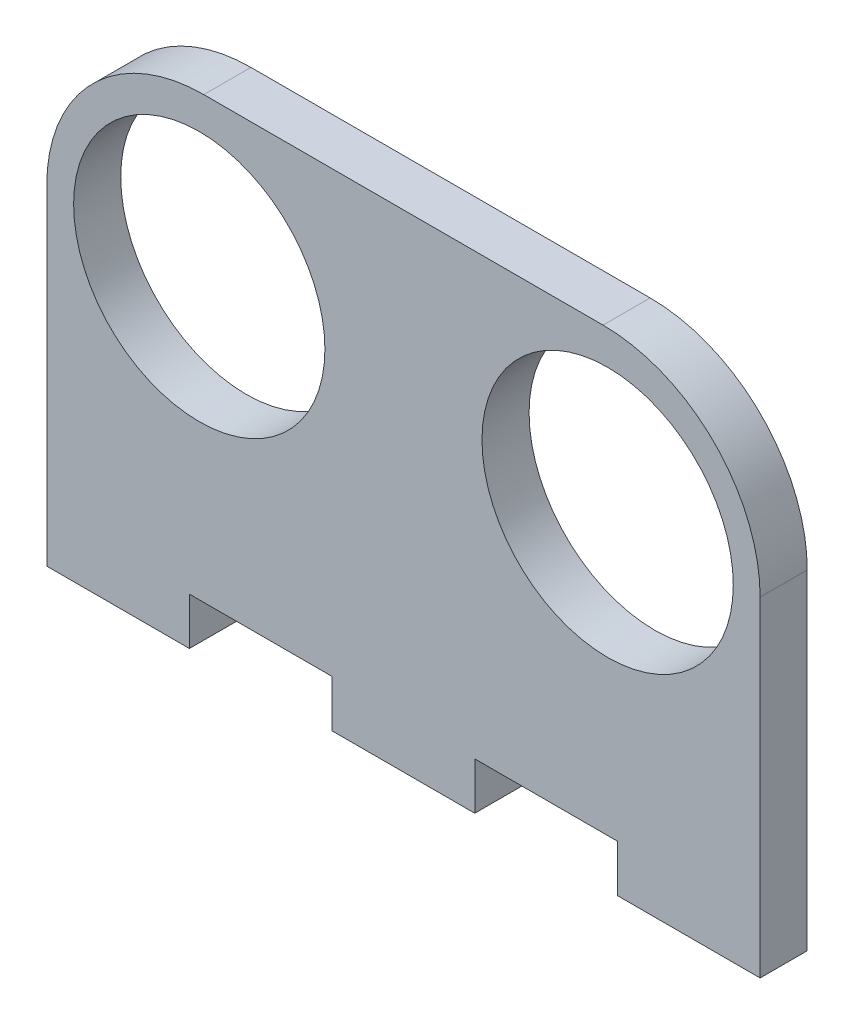
SolidWorks part; units mm, degrees
material "Arce"
ref_plane "Alzado" through (0, 0, 0) normal (0, 0, 1) x (1, 0, 0)
ref_plane "Planta" through (0, 0, 0) normal (0, 1, 0) x (1, 0, 0)
ref_plane "Vista lateral" through (0, 0, 0) normal (1, 0, 0) x (0, 0, -1)
sketch "Croquis1" plane through (0, 0, 0) normal (0, 0, 1) x (1, 0, 0)
  line L1 (-22.71, -10.17) -> (22.71, -10.17)
  line L2 (-22.71, -10.17) -> (-22.71, 7.83)
  line L3 (-12.71, 17.83) -> (12.71, 17.83)
  line L4 (22.71, -10.17) -> (22.71, 7.83)
  line L5 (-22.71, -10.17) -> (22.71, 17.83) construction
  line L6 (-22.71, 17.83) -> (22.71, -10.17) construction
  arc A0 (-22.71, 7.83) -> (-12.71, 17.83) centre (-12.71, 7.83) cw
  arc A1 (12.71, 17.83) -> (22.71, 7.83) centre (12.71, 7.83) cw
  point P0 (0, 3.83)
  dimension "D3" = 10
  dimension "D1" = 28
  dimension "D2" = 45.42
extrude "Saliente-Extruir1" add sketch "Croquis1" along normal blind 3
sketch "Croquis2" plane through (0, 0, 3) normal (0, 0, 1) x (1, 0, 0)
  line L1 (-22.71, 7.83) -> (-22.71, -10.17) construction
  line L2 (12.71, 17.83) -> (-12.71, 17.83) construction
  line L3 (-22.71, -10.17) -> (22.71, -10.17) construction
  line L4 (22.71, -10.17) -> (22.71, 7.83) construction
  circle A0 centre (-21.41, 16.53) radius 0.8
  circle A1 centre (21.41, 16.53) radius 0.8
  circle A2 centre (21.41, -8.87) radius 0.8
  circle A3 centre (-21.41, -8.87) radius 0.8
  dimension "D1" = 1.6
  dimension "D2" = 1.6
  dimension "D3" = 1.6
  dimension "D4" = 1.6
  dimension "D5" = 1.3
  dimension "D6" = 1.3
  dimension "D7" = 1.3
  dimension "D8" = 1.3
  dimension "D9" = 1.3
  dimension "D10" = 1.3
  dimension "D11" = 1.3
  dimension "D12" = 1.3
sketch "Croquis3" plane through (0, 0, 3) normal (0, 0, 1) x (1, 0, 0)
  line L0 (12.71, 17.83) -> (-12.71, 17.83) construction
  line L1 (-22.71, 7.83) -> (-22.71, -10.17) construction
  line L2 (22.71, -10.17) -> (22.71, 7.83) construction
  circle A0 centre (-13, 7.65) radius 8
  circle A1 centre (13, 7.65) radius 8
  dimension "D1" = 16
  dimension "D2" = 16
  dimension "D3" = 10.18
  dimension "D4" = 10.18
  dimension "D5" = 9.71
  dimension "D6" = 9.71
extrude "Cortar-Extruir2" cut sketch "Croquis3" against normal blind 3
sketch "Croquis4" plane through (0, 0, 3) normal (0, 0, 1) x (1, 0, 0)
  line L0 (22.71, -10.17) -> (22.71, 7.83) construction
  line L1 (-5.41, 17.83) -> (5.41, 17.83)
  line L2 (-5.41, 17.83) -> (-5.41, 13.43)
  line L3 (-5.41, 13.43) -> (5.41, 13.43)
  line L4 (5.41, 17.83) -> (5.41, 13.43)
  line L5 (12.71, 17.83) -> (-12.71, 17.83) construction
  dimension "D1" = 4.4
  dimension "D2" = 10.82
  dimension "D3" = 17.3
sketch "Croquis5" plane through (0, -10.17, 0) normal (0, -1, 0) x (1, 0, 0)
  line L0 (-22.71, 0) -> (22.71, 0) construction
  line L1 (-22.71, 3) -> (-13.626, 3)
  line L2 (-22.71, 3) -> (-22.71, 0)
  line L3 (-22.71, 0) -> (-13.626, 0)
  line L4 (-13.626, 3) -> (-13.626, 0)
  line L6 (-13.626, 3) -> (-4.542, 3)
  line L7 (-13.626, 3) -> (-13.626, 0)
  line L8 (-13.626, 0) -> (-4.542, 0)
  line L9 (-4.542, 3) -> (-4.542, 0)
  line L10 (-4.542, 3) -> (4.542, 3)
  line L11 (-4.542, 3) -> (-4.542, 0)
  line L12 (-4.542, 0) -> (4.542, 0)
  line L13 (4.542, 3) -> (4.542, 0)
  line L14 (4.542, 3) -> (22.71, 3)
  line L15 (4.542, 3) -> (4.542, 0)
  line L16 (4.542, 0) -> (22.71, 0)
  line L17 (22.71, 3) -> (22.71, 0)
  line L18 (4.542, 3) -> (13.626, 3)
  line L19 (4.542, 3) -> (4.542, 0)
  line L20 (4.542, 0) -> (13.626, 0)
  line L21 (13.626, 3) -> (13.626, 0)
  line M18 (-22.71, 0) -> (22.71, 0)
  line M19 (22.71, 0) -> (22.71, 3)
  line M20 (22.71, 3) -> (-22.71, 3)
  line M21 (-22.71, 3) -> (-22.71, 0)
  dimension "D1" = 9.084
  dimension "D2" = 9.084
  dimension "D3" = 9.084
  dimension "D4" = 9.084
extrude "Saliente-Extruir2" add sketch "Croquis5" along normal blind 3 contours L4 M20 M21 M18 | L13 L9 M20 M18 | L21 L16 M20 M19
